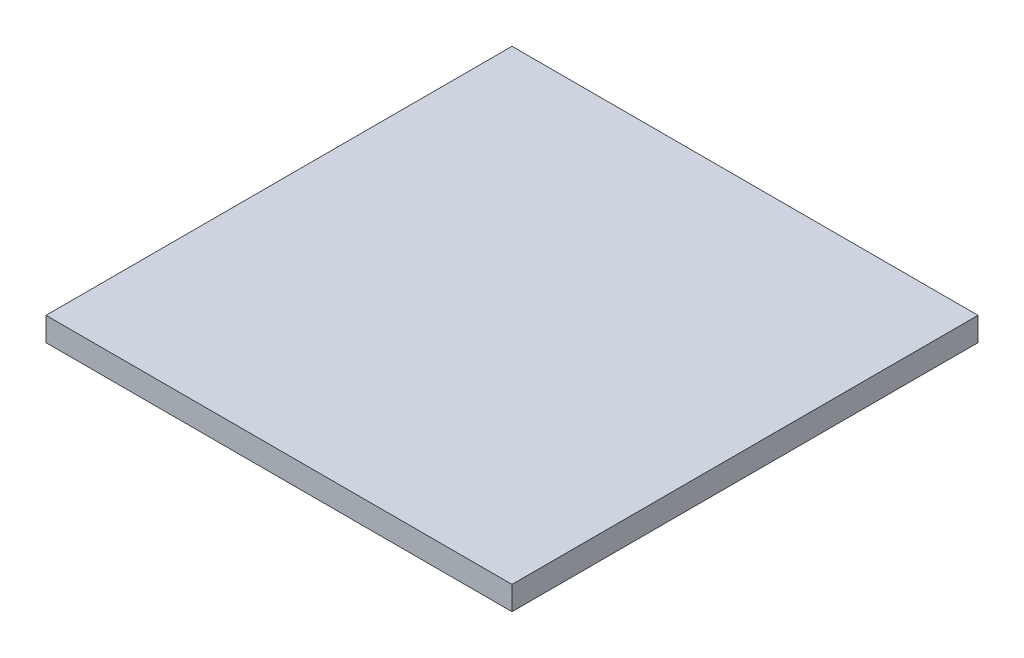
SolidWorks part; units mm, degrees
ref_plane "Front Plane" through (0, 0, 0) normal (0, 0, 1) x (1, 0, 0)
ref_plane "Top Plane" through (0, 0, 0) normal (0, 1, 0) x (1, 0, 0)
ref_plane "Right Plane" through (0, 0, 0) normal (1, 0, 0) x (0, 0, -1)
sketch "Sketch1" plane through (0, 0, 0) normal (0, 1, 0) x (1, 0, 0)
  line L1 (-22.2032, 19.6493) -> (7.2968, 19.6493)
  line L2 (-22.2032, 19.6493) -> (-22.2032, -9.8507)
  line L3 (-22.2032, -9.8507) -> (7.2968, -9.8507)
  line L4 (7.2968, 19.6493) -> (7.2968, -9.8507)
  dimension "D1" = 29.5
  dimension "D2" = 29.5
extrude "Boss-Extrude1" add sketch "Sketch1" along normal blind 1.5
